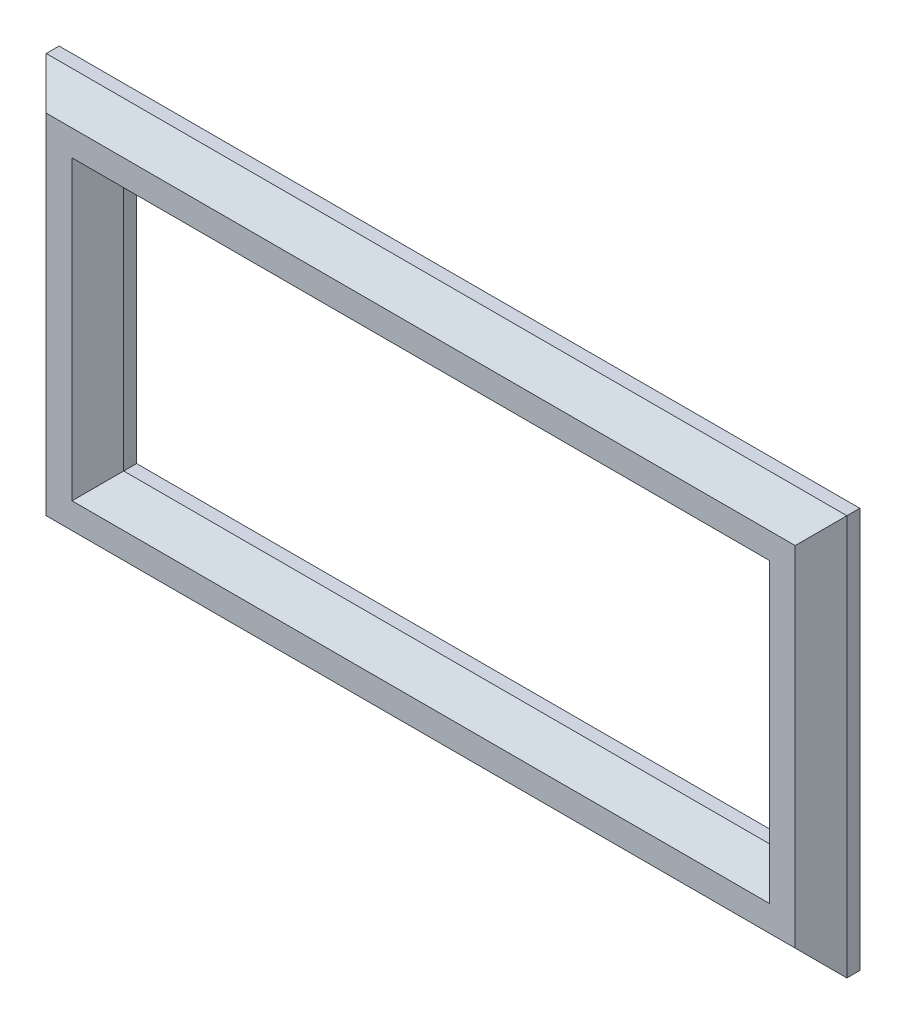
SolidWorks part; units mm, degrees
ref_plane "Plan de face" through (0, 0, 0) normal (0, 0, 1) x (1, 0, 0)
ref_plane "Plan de dessus" through (0, 0, 0) normal (0, 1, 0) x (1, 0, 0)
ref_plane "Plan de droite" through (0, 0, 0) normal (1, 0, 0) x (0, 0, -1)
sketch "Esquisse1" plane through (0, 0, 0) normal (0, 0, 1) x (1, 0, 0)
  line L0 (6, -6) -> (-56, -6)
  line L1 (0, 0) -> (-50, 0)
  line L2 (0, 0) -> (0, 19)
  line L3 (0, 19) -> (-50, 19)
  line L4 (-50, 0) -> (-50, 19)
  line L5 (-56, -6) -> (-56, 25)
  line L6 (6, 25) -> (-56, 25)
  line L7 (6, -6) -> (6, 25)
  dimension "D1" = 6
extrude "Boss.-Extru.1" add sketch "Esquisse1" along normal blind 3
chamfer "Chanfrein1" distance 2 angle 45 8 edges at (-50, 9.5, 3) (-25, 0, 3) (0, 9.5, 3) (-25, 19, 3) (-25, -6, 3) (-56, 9.5, 3) (-25, 25, 3) (6, 9.5, 3)
